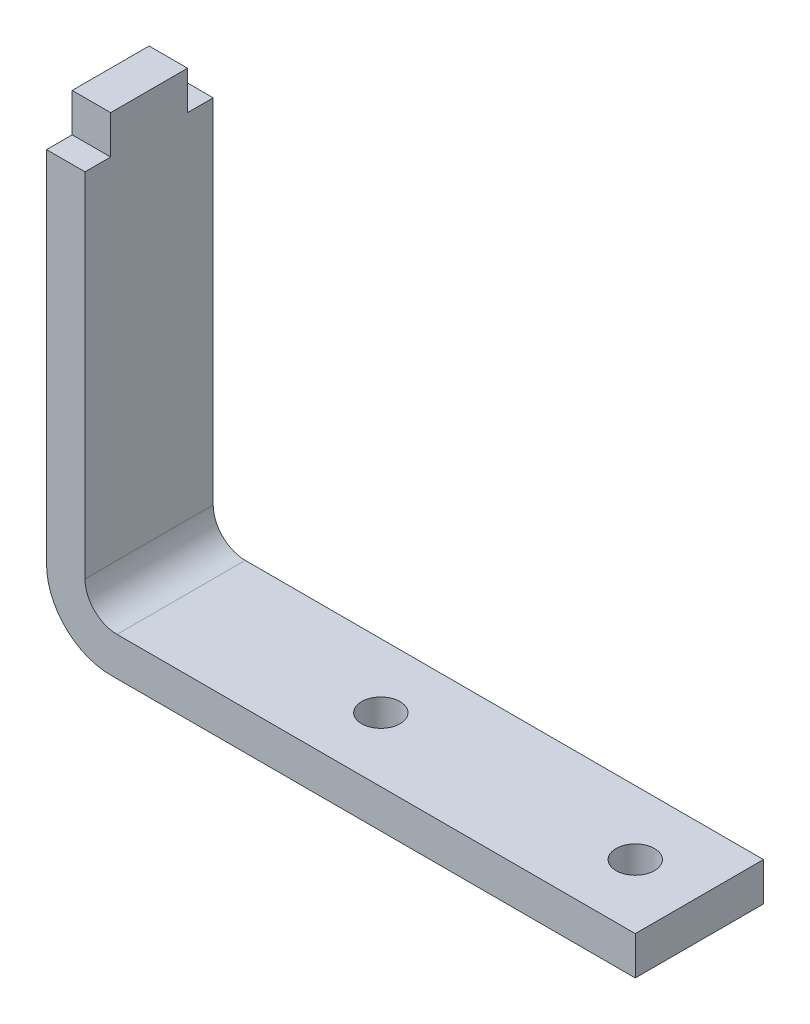
SolidWorks part; units mm, degrees
ref_plane "Front Plane" through (0, 0, 0) normal (0, 0, 1) x (1, 0, 0)
ref_plane "Top Plane" through (0, 0, 0) normal (0, 1, 0) x (1, 0, 0)
ref_plane "Right Plane" through (0, 0, 0) normal (1, 0, 0) x (0, 0, -1)
sketch "Sketch5" plane through (0, 0, 0) normal (0, 0, 1) x (1, 0, 0)
  line L0 (0, 0) -> (-59, 0)
  line L1 (-59, 0) -> (-59, 33)
  line L2 (-59, 33) -> (-56, 33)
  line L3 (-56, 33) -> (-56, 3)
  line L4 (-56, 3) -> (0, 3)
  line L5 (0, 3) -> (0, 0)
  dimension "D1" = 3
  dimension "D2" = 30
  dimension "D3" = 56
extrude "Boss-Extrude2" add sketch "Sketch5" against normal mid plane 10 contours L5 L4 L3 L2 L1 L0
sketch "Sketch8" plane through (0, 3, 0) normal (0, 1, 0) x (1, 0, 0)
  line L0 (-37.925, 0) -> (-18.075, 0) construction
  line L1 (-56, -5) -> (0, -5) construction
  circle A0 centre (-18.075, 0) radius 1.5
  circle A1 centre (-37.925, 0) radius 1.5
  point P6 (-28, -5)
  point P8 (-28, 0)
  dimension "D3" = 3
  dimension "D1" = 19.85
extrude "Cut-Extrude3" cut sketch "Sketch8" against normal blind 3
fillet "Fillet7" radius 5 1 edges at (-59, 0, 0)
fillet "Fillet8" radius 2.5 1 edges at (-56, 3, 0)
sketch "Sketch9" plane through (0, 3, 0) normal (0, 1, 0) x (1, 0, 0)
  line L0 (-53.5, 5) -> (0, 5) construction
  line L1 (0, -5) -> (-13.075, -5)
  line L2 (0, -5) -> (0, 5)
  line L3 (0, 5) -> (-13.075, 5)
  line L4 (-13.075, -5) -> (-13.075, 5)
  circle A0 centre (-18.075, 0) radius 1.5 construction
  dimension "D1" = 5
extrude "Cut-Extrude4" cut sketch "Sketch9" against normal blind 3
sketch "Sketch11" plane through (0, 33, 0) normal (0, 1, 0) x (1, 0, 0)
  line L0 (-56, 5) -> (-56, -5) construction
  line L1 (-56, 3) -> (-59, 3)
  line L2 (-56, 3) -> (-56, -3)
  line L3 (-56, -3) -> (-59, -3)
  line L4 (-59, 3) -> (-59, -3)
  line L5 (-59, 5) -> (-59, -5) construction
  point P8 (-59, 0)
  point P9 (-59, 0)
  dimension "D1" = 6
extrude "Boss-Extrude4" add sketch "Sketch11" along normal blind 3 contours L1 L4 L3 L2
